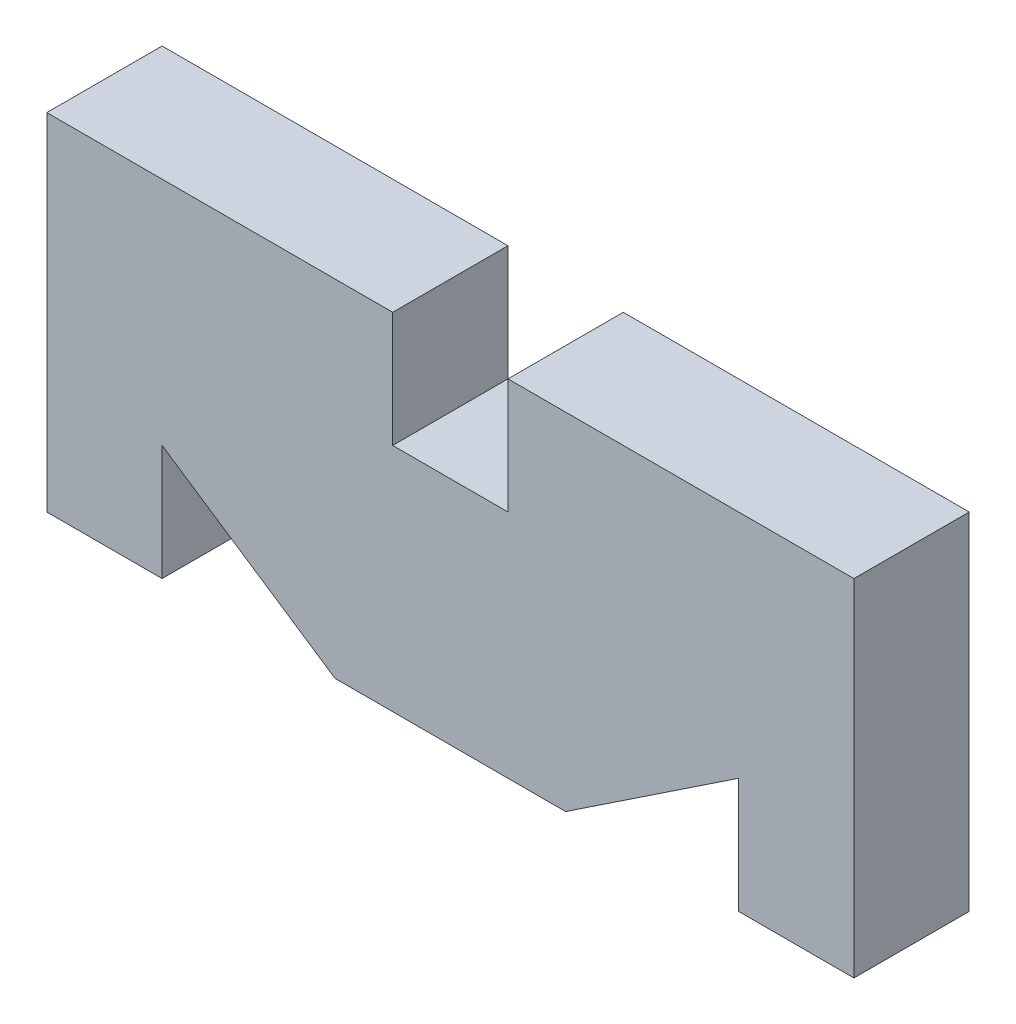
SolidWorks part; units mm, degrees
ref_plane "Front Plane" through (0, 0, 0) normal (0, 0, 1) x (1, 0, 0)
ref_plane "Top Plane" through (0, 0, 0) normal (0, 1, 0) x (1, 0, 0)
ref_plane "Right Plane" through (0, 0, 0) normal (1, 0, 0) x (0, 0, -1)
sketch "Sketch1" plane through (0, 0, 0) normal (0, 0, 1) x (1, 0, 0)
  line L1 (-35, -15) -> (-25, -15)
  line L2 (-35, -15) -> (-35, 15)
  line L3 (-35, 15) -> (-5, 15)
  line L4 (35, -15) -> (35, 15)
  line L5 (-35, -15) -> (-11.6667, -5) construction
  line L6 (-35, 15) -> (-11.6667, 5) construction
  line L7 (5, 15) -> (5, 5)
  line L9 (25, -5) -> (10, -15)
  line L10 (-25, -5) -> (-25, -15)
  line L11 (25, -5) -> (25, -15)
  line L13 (25, -15) -> (35, -15)
  line L14 (-25, -5) -> (-10, -15)
  line L15 (-10, -15) -> (10, -15)
  line L16 (10, -4.2857) -> (10, -5)
  line L18 (-5, 15) -> (-5, 5)
  line L19 (11.6667, -5) -> (35, -15) construction
  line L20 (5, 2.1429) -> (6.6391, 2.8453) construction
  line L21 (-5, 5) -> (5, 5)
  line L23 (5, 2.1429) -> (6.6391, 2.8453) construction
  line L24 (5, 15) -> (35, 15)
  point P0 (0, 0)
  dimension "D1" = 70
  dimension "D2" = 30
extrude "Boss-Extrude1" add sketch "Sketch1" along normal blind 10
